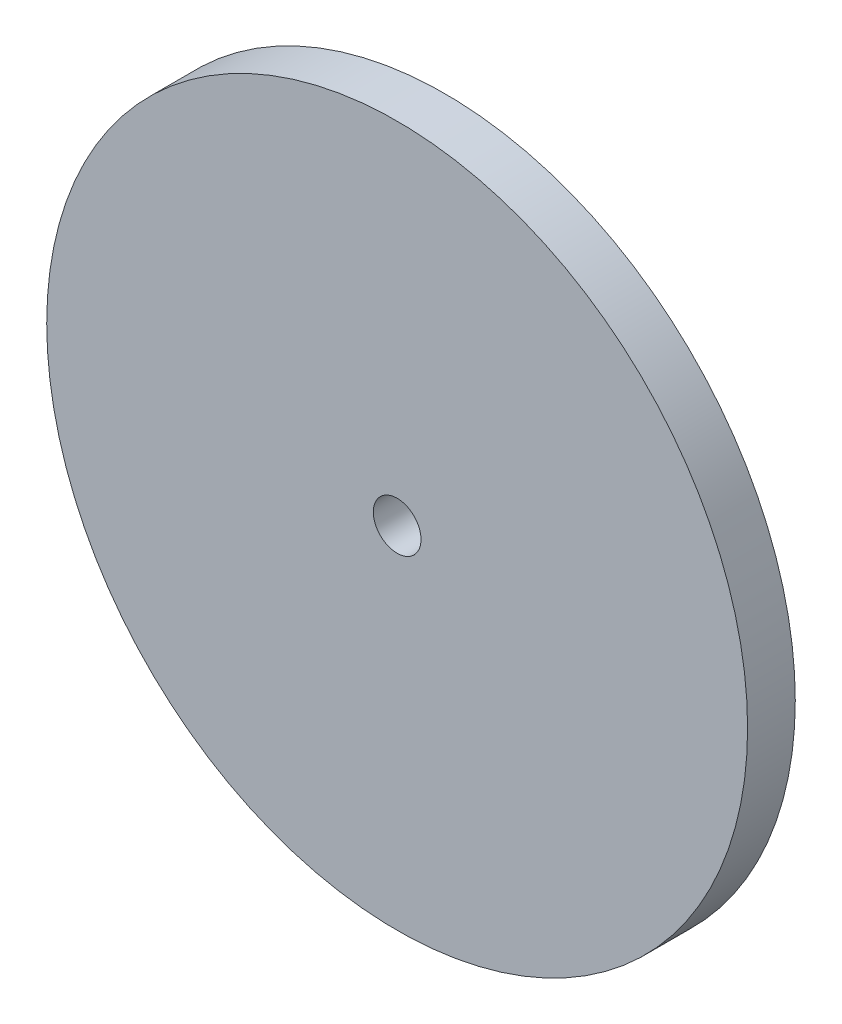
SolidWorks part; units mm, degrees
material "AISI 316 Annealed Stainless Steel Bar (SS)"
ref_plane "Front Plane" through (0, 0, 0) normal (0, 0, 1) x (1, 0, 0)
ref_plane "Top Plane" through (0, 0, 0) normal (0, 1, 0) x (1, 0, 0)
ref_plane "Right Plane" through (0, 0, 0) normal (1, 0, 0) x (0, 0, -1)
sketch "Sketch1" plane through (0, 0, 0) normal (0, 0, 1) x (1, 0, 0)
  circle A0 centre (0, 0) radius 7.35
  circle A1 centre (0, 0) radius 0.5
  dimension "D1" = 14.7
  dimension "D2" = 1
extrude "Boss-Extrude1" add sketch "Sketch1" along normal blind 1
